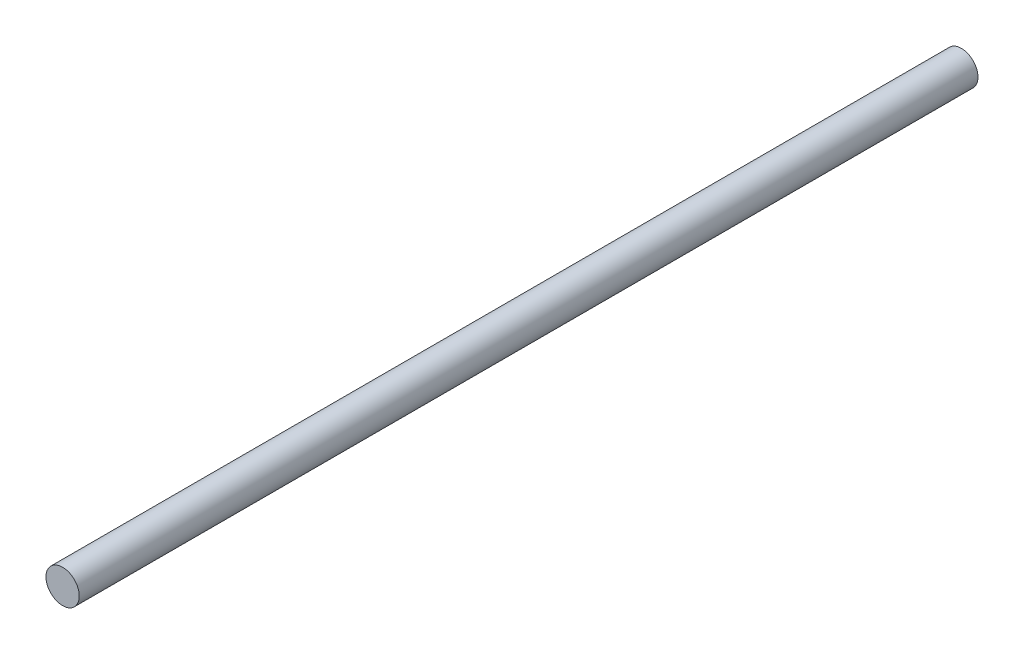
SolidWorks part; units mm, degrees
ref_plane "Front Plane" through (0, 0, 0) normal (0, 0, 1) x (1, 0, 0)
ref_plane "Top Plane" through (0, 0, 0) normal (0, 1, 0) x (1, 0, 0)
ref_plane "Right Plane" through (0, 0, 0) normal (1, 0, 0) x (0, 0, -1)
sketch "Sketch1" plane through (0, 0, 0) normal (0, 0, 1) x (1, 0, 0)
  circle A0 centre (0, 0) radius 6.35
  dimension "D1" = 12.7
extrude "Boss-Extrude1" add sketch "Sketch1" along normal blind 342.9
